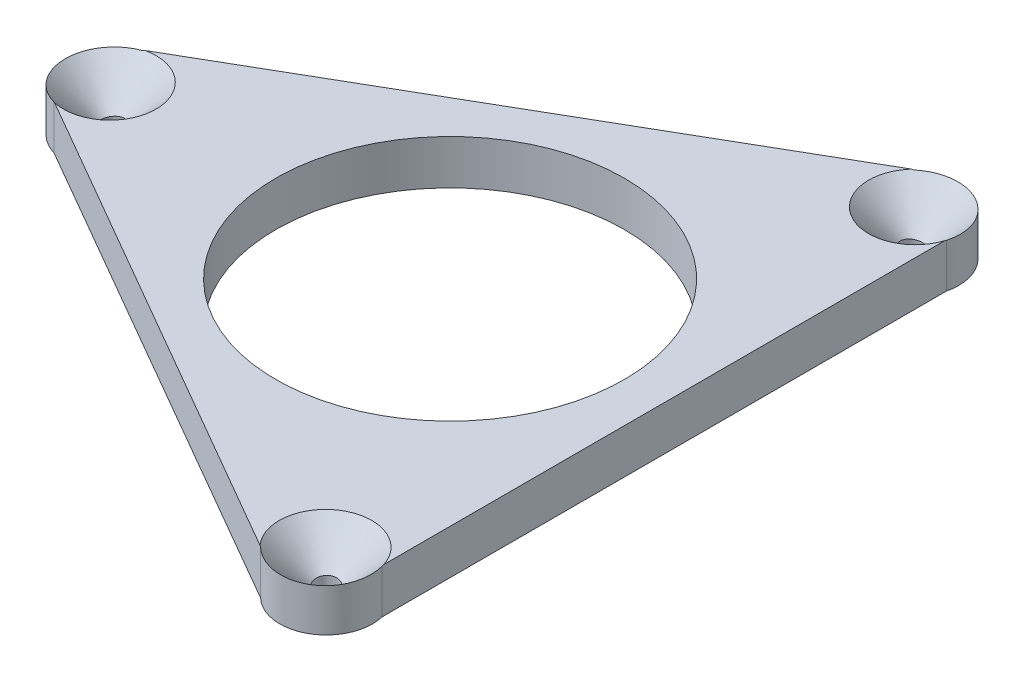
SolidWorks part; units mm, degrees
ref_plane "Front Plane" through (0, 0, 0) normal (0, 0, 1) x (1, 0, 0)
ref_plane "Top Plane" through (0, 0, 0) normal (0, 1, 0) x (1, 0, 0)
ref_plane "Right Plane" through (0, 0, 0) normal (1, 0, 0) x (0, 0, -1)
sketch "Sketch1" plane through (0, 0, 0) normal (0, 1, 0) x (1, 0, 0)
  line L0 (-11.59, 1.5875) -> (-0.6409, 1.5875) construction
  line L1 (-11.59, 0) -> (0, 0) construction
  line L2 (7.3371, 9.6602) -> (4.6974, 11.1842) construction
  line L3 (-12.0345, -1.524) -> (-0.9403, -1.524) construction
  line L4 (7.1698, 9.2435) -> (1.6953, -0.2387) construction
  line L5 (0, 0) -> (0, -6.477) construction
  line L6 (4.6974, 11.1842) -> (-0.8496, 1.5764) construction
  line L7 (4.6974, -11.1842) -> (7.3371, -9.6602) construction
  line L8 (4.4202, -10.831) -> (-1.0544, -1.3488) construction
  line L9 (7.3371, -9.6602) -> (1.79, -0.0524) construction
  line L10 (-12.0345, 1.524) -> (-12.0345, -1.524) construction
  line L11 (5.795, 10.0372) -> (0, 0) construction
  line L12 (0, 0) -> (5.795, -10.0372) construction
  line L13 (-12.0345, 1.524) -> (4.6974, 11.1842)
  line L14 (7.3371, 9.6602) -> (7.3371, -9.6602)
  line L15 (4.6974, -11.1842) -> (-12.0345, -1.524)
  circle A0 centre (0, 0) radius 5.969
  circle A1 centre (0, 0) radius 6.477
  circle A2 centre (-11.59, 0) radius 1.5875
  circle A7 centre (5.795, 10.0372) radius 1.5875
  circle A8 centre (5.795, -10.0372) radius 1.5875
  point P26 (0, 0)
  point P29 (0, 0)
  point P33 (0, 0)
  dimension "D4" = 11.938
  dimension "D5" = 12.954
  dimension "D1" = 3.175
  dimension "D2" = 3
  dimension "D3" = 6.477
extrude "Boss-Extrude1" add sketch "Sketch1" along normal blind 1.524
sketch "Sketch2" plane through (0, 1.524, 0) normal (0, 1, 0) x (1, 0, 0)
  line L4 (0, 0) -> (-13.208, 0) construction
  arc A0 (-11.6522, -1.5875) -> (-11.6522, 1.5875) centre (-11.6522, 0) ccw
  circle A1 centre (-11.6522, 0) radius 1.5875
  point P7 (-11.6522, 0)
  dimension "D1" = 11.6522
  dimension "D2" = 3.175
extrude "Cut-Extrude1" cut sketch "Sketch2" against normal blind 2.54 draft 45 contours A1
sketch "Sketch3" plane through (0, 0, 0) normal (1, 0, 0) x (0, 0, -1)
  line L0 (0, 0) -> (0, 5.5164) construction
pattern_circular "CirPattern1" count 3 over 360 about axis through (0, 0, 0) along (0, 1, 0) of "Cut-Extrude1"
sketch "Sketch4" plane through (0, 0, 0) normal (0, -1, 0) x (1, 0, 0)
  line L0 (0, 0) -> (5.795, -10.0372) construction
  circle A0 centre (5.795, -10.0372) radius 0.381
  circle A2 centre (-11.59, 0) radius 0.381
  circle A3 centre (5.795, 10.0372) radius 0.381
  point P2 (5.4019, -9.4104)
  point P3 (5.8261, -10.1546)
  point P9 (5.795, -10.0372)
  point P10 (5.7626, -10.0911)
  point P14 (0, 0)
  point P16 (5.795, -10.0372)
  point P17 (5.7933, -10.0355)
  point P18 (5.7707, -10.0586)
  point P20 (5.795, -10.0372)
  point P22 (0, 0)
  dimension "D1" = 0.762
  dimension "D2" = 3
extrude "Cut-Extrude2" cut sketch "Sketch4" against normal blind 12.7
